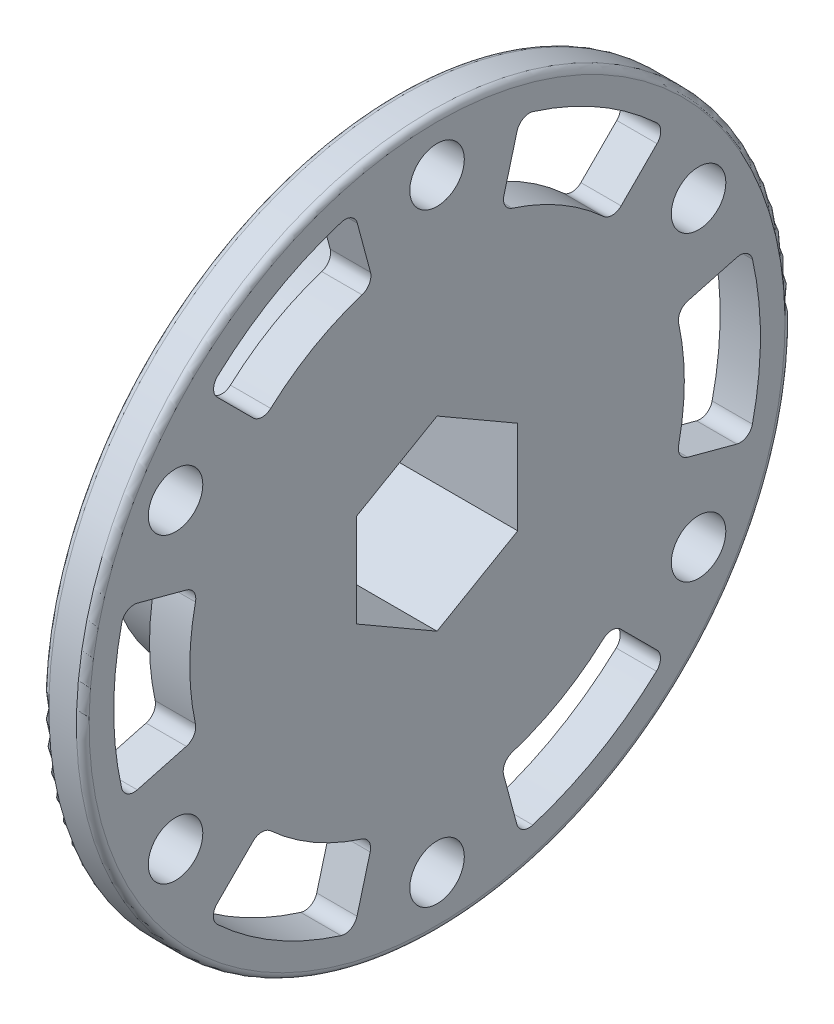
SolidWorks part; units mm, degrees
ref_plane "Front Plane" through (0, 0, 0) normal (0, 0, 1) x (1, 0, 0)
ref_plane "Top Plane" through (0, 0, 0) normal (0, 1, 0) x (1, 0, 0)
ref_plane "Right Plane" through (0, 0, 0) normal (1, 0, 0) x (0, 0, -1)
ref_plane "Plane1" through (0, 0, 0) normal (0, 0, -1) x (-1, 0, 0)
sketch "Sketch1" plane through (0, 0, 0) normal (0, 0, -1) x (-1, 0, 0)
  line L0 (-12.7, 27.94) -> (-12.7, 0)
  line L1 (-12.7, 0) -> (-9.525, 0)
  line L2 (-9.525, 0) -> (-9.525, 27.94)
  line L3 (-9.525, 27.94) -> (-12.7, 27.94)
  line L4 (-12.7, 0) -> (-9.525, 0) construction
revolve "Revolve1" add sketch "Sketch1" angle 360 about L4
sketch "Sketch2" plane through (9.525, 0, 0) normal (-1, 0, 0) x (0, 0, 1)
  line L0 (-13.8065, -13.7706) -> (-18.0492, -18.0133)
  line L1 (-6.5508, -24.6442) -> (-4.9979, -18.8486)
  arc A0 (-4.9979, -18.8486) -> (-13.8065, -13.7706) centre (0, 0) cw
  arc A1 (-18.0492, -18.0133) -> (-6.5508, -24.6442) centre (0, 0) ccw
extrude "Cut-Extrude1" cut sketch "Sketch2" against normal through all
sketch "Sketch3" plane through (9.525, 0, 0) normal (-1, 0, 0) x (0, 0, 1)
  line L0 (5.0224, -18.8421) -> (6.5753, -24.6377)
  line L1 (18.0671, -17.9953) -> (13.8245, -13.7526)
  arc A0 (13.8245, -13.7526) -> (5.0224, -18.8421) centre (0, 0) cw
  arc A1 (6.5753, -24.6377) -> (18.0671, -17.9953) centre (0, 0) ccw
extrude "Cut-Extrude2" cut sketch "Sketch3" against normal through all
sketch "Sketch4" plane through (9.525, 0, 0) normal (-1, 0, 0) x (0, 0, 1)
  line L0 (18.829, -5.0715) -> (24.6245, -6.6244)
  line L1 (24.6179, 6.6489) -> (18.8223, 5.096)
  arc A0 (18.8223, 5.096) -> (18.829, -5.0715) centre (0, 0) cw
  arc A1 (24.6245, -6.6244) -> (24.6179, 6.6489) centre (0, 0) ccw
extrude "Cut-Extrude3" cut sketch "Sketch4" against normal through all
sketch "Sketch5" plane through (9.525, 0, 0) normal (-1, 0, 0) x (0, 0, 1)
  line L0 (13.8065, 13.7706) -> (18.0492, 18.0133)
  line L1 (6.5508, 24.6442) -> (4.9979, 18.8486)
  arc A0 (4.9979, 18.8486) -> (13.8065, 13.7706) centre (0, 0) cw
  arc A1 (18.0492, 18.0133) -> (6.5508, 24.6442) centre (0, 0) ccw
extrude "Cut-Extrude4" cut sketch "Sketch5" against normal through all
sketch "Sketch6" plane through (9.525, 0, 0) normal (-1, 0, 0) x (0, 0, 1)
  line L0 (-24.6179, -6.6489) -> (-18.8223, -5.096)
  line L1 (-18.829, 5.0715) -> (-24.6245, 6.6244)
  arc A0 (-18.8223, -5.096) -> (-18.829, 5.0715) centre (0, 0) cw
  arc A1 (-24.6245, 6.6244) -> (-24.6179, -6.6489) centre (0, 0) ccw
extrude "Cut-Extrude5" cut sketch "Sketch6" against normal through all
sketch "Sketch7" plane through (12.7, 0, 0) normal (1, 0, 0) x (0, 0, -1)
  line L0 (6.5753, 24.6377) -> (5.0224, 18.8421)
  line L1 (13.8245, 13.7526) -> (18.0671, 17.9953)
  arc A0 (18.0671, 17.9953) -> (6.5753, 24.6377) centre (0, 0) ccw
  arc A1 (5.0224, 18.8421) -> (13.8245, 13.7526) centre (0, 0) cw
extrude "Cut-Extrude6" cut sketch "Sketch7" against normal through all
sketch "Sketch8" plane through (9.525, 0, 0) normal (-1, 0, 0) x (0, 0, 1)
  circle A0 centre (0, 0) radius 14.2949
extrude "Boss-Extrude1" add sketch "Sketch8" along normal blind 9.525
sketch "Sketch9" plane through (12.7, 0, 0) normal (1, 0, 0) x (0, 0, -1)
  line L0 (-6.3627, 3.6735) -> (-6.3627, -3.6735)
  line L1 (-6.3627, -3.6735) -> (0, -7.347)
  line L2 (0, -7.347) -> (6.3627, -3.6735)
  line L3 (6.3627, -3.6735) -> (6.3627, 3.6735)
  line L4 (6.3627, 3.6735) -> (0, 7.347)
  line L5 (0, 7.347) -> (-6.3627, 3.6735)
extrude "Cut-Extrude7" cut sketch "Sketch9" against normal through all
hole_wizard "Ø4.3 (4.3) Diameter Hole1" positions "Sketch11" profile "Sketch10" hole size "Ø4.3" standard "ANSI Metric"
sketch "Sketch11" plane through (12.7, 0, 0) normal (1, 0, 0) x (0, 0, -1)
  point P0 (20.6222, 11.9063)
  point P1 (20.6222, -11.9062)
  point P2 (0, -23.8125)
  point P3 (-20.6222, -11.9063)
  point P4 (-20.6222, 11.9062)
  point P5 (0, 23.8125)
sketch "Sketch10" plane through (12.7, 11.9063, -20.6222) normal (0, 1, 0) x (0, 0, -1)
  line L0 (0, 0) -> (0, 12.7)
  line L1 (0, 12.7) -> (2.15, 12.7)
  line L2 (2.15, 12.7) -> (2.15, 0)
  line L5 (2.15, 0) -> (0, 0)
  line L11 (0, -6.35) -> (0, 107.95) construction
  dimension "Thru Hole Dia." = 4.3
  dimension "Thru Hole Depth" = 12.7
chamfer "Chamfer1" distance 1 angle 45 1 edges at (0, -14.2949, 0)
fillet "Fillet1" radius 0.5 2 edges at (12.7, -27.94, 0) (9.525, -27.94, 0)
fillet "Fillet2" radius 1 24 edges at (11.1125, 6.6489, 24.6179) (11.1125, -17.9953, 18.0671) (11.1125, 24.6442, 6.5508) (11.1125, -18.8421, 5.0224) (11.1125, 18.8421, -5.0224) (11.1125, -5.0715, 18.829) (11.1125, 24.6377, -6.5753) (11.1125, 13.7706, 13.8065) (11.1125, 17.9953, -18.0671) (11.1125, -18.8486, -4.9979) (11.1125, 13.7526, -13.8245) (11.1125, -24.6377, 6.5753) (11.1125, 5.0715, -18.829) (11.1125, -13.7526, 13.8245) (11.1125, 6.6244, -24.6245) (11.1125, -6.6244, 24.6245) (11.1125, -6.6489, -24.6179) (11.1125, 5.096, 18.8223) (11.1125, -5.096, -18.8223) (11.1125, 18.0133, 18.0492) (11.1125, -13.7706, -13.8065) (11.1125, 18.8486, 4.9979) (11.1125, -18.0133, -18.0492) (11.1125, -24.6442, -6.5508)
fillet "Fillet3" radius 1.27 1 edges at (9.525, -14.2949, 0)
